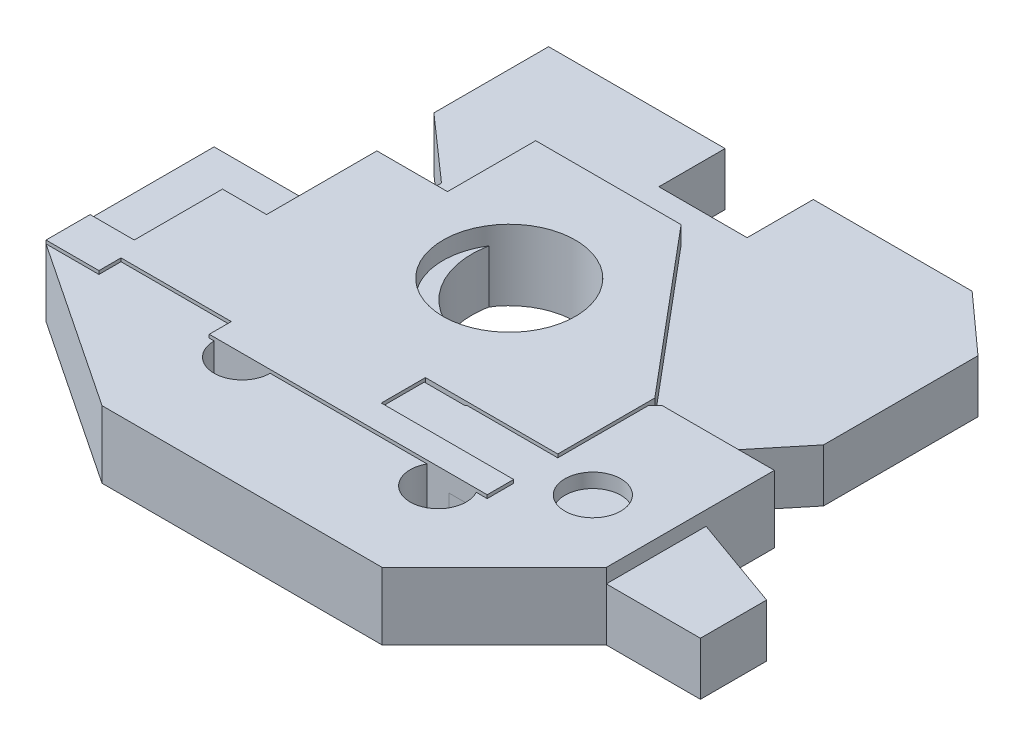
SolidWorks part; units mm, degrees
ref_plane "Front Plane" through (0, 0, 0) normal (0, 0, 1) x (1, 0, 0)
ref_plane "Top Plane" through (0, 0, 0) normal (0, 1, 0) x (1, 0, 0)
ref_plane "Right Plane" through (0, 0, 0) normal (1, 0, 0) x (0, 0, -1)
sketch "Sketch1" plane through (0, 0, 0) normal (0, 1, 0) x (1, 0, 0)
  line L0 (0, 0) -> (50, 0)
  line L1 (50, 0) -> (44, 9.42)
  line L2 (44, 9.42) -> (97.33, 9.42)
  line L3 (97.33, 9.42) -> (91.33, 0)
  line L4 (91.33, 0) -> (148.33, 0)
  line L5 (148.33, 0) -> (148.33, 15)
  line L6 (148.33, 15) -> (106.33, 30)
  line L7 (106.33, 30) -> (124.33, 51.92)
  line L8 (124.33, 51.92) -> (124.33, 86.92)
  line L9 (124.33, 86.92) -> (111, 98.92)
  line L10 (111, 98.92) -> (75, 98.92)
  line L11 (75, 98.92) -> (75, 83.92)
  line L12 (75, 83.92) -> (55, 83.92)
  line L13 (55, 83.92) -> (55, 98.92)
  line L14 (55, 98.92) -> (15, 98.92)
  line L15 (15, 98.92) -> (15, 72.92)
  line L16 (15, 72.92) -> (29.6447, 60)
  line L17 (29.6447, 60) -> (29.6447, 40)
  line L18 (29.6447, 40) -> (12, 20)
  line L19 (12, 20) -> (0, 20)
  line L20 (0, 20) -> (0, 0)
  circle A0 centre (65, 49.5) radius 18
  dimension "D24" = 36
  dimension "D1" = 50
  dimension "D2" = 57
  dimension "D3" = 15
  dimension "D4" = 20
  dimension "D5" = 40
  dimension "D6" = 26
  dimension "D7" = 20
  dimension "D8" = 12
  dimension "D9" = 6
  dimension "D10" = 6
  dimension "D11" = 148.33
  dimension "D12" = 9.42
  dimension "D13" = 30
  dimension "D14" = 98.92
  dimension "D15" = 47
  dimension "D16" = 12
  dimension "D17" = 13.33
  dimension "D18" = 109.33
  dimension "D19" = 20
  dimension "D20" = 20
  dimension "D21" = 42
  dimension "D22" = 15
  dimension "D23" = 15
  dimension "D25" = 50
  dimension "D26" = 49.5
extrude "Boss-Extrude1" add sketch "Sketch1" along normal blind 12
sketch "Sketch3" plane through (0, 0, 0) normal (0, 1, 0) x (1, 0, 0)
  line L0 (0, 0) -> (0, 38.1)
  line L1 (0, 38.1) -> (25.4, 38.1)
  line L2 (25.4, 38.1) -> (47.752, 15.748)
  line L3 (47.752, 15.748) -> (79.248, 15.748)
  line L4 (79.248, 15.748) -> (101.6, 38.1)
  line L5 (101.6, 38.1) -> (127, 38.1)
  line L6 (127, 38.1) -> (127, 0)
  line L7 (127, 0) -> (101.6, -25.4)
  line L8 (101.6, -25.4) -> (38.1, -25.4)
  line L9 (38.1, -25.4) -> (0, 0)
  circle A0 centre (19.05, 19.05) radius 6.35
  circle A1 centre (44.45, 0) radius 6.35
  circle A2 centre (91.948, -3.048) radius 6.35
  circle A3 centre (111.252, 12.7) radius 6.35
  point P19 (0, 0)
  point P20 (0, 0)
  point P21 (0, 0)
  point P22 (0, 0)
  point P23 (0, 0)
  point P24 (0, 0)
  point P25 (0, 0)
  dimension "D12" = 12.7
  dimension "D13" = 12.7
  dimension "D14" = 12.7
  dimension "D15" = 12.7
  dimension "D1" = 25.4
  dimension "D2" = 25.4
  dimension "D3" = 63.5
  dimension "D4" = 38.1
  dimension "D5" = 45
  dimension "D6" = 63.5
  dimension "D7" = 127
  dimension "D8" = 47.752
  dimension "D9" = 47.752
  dimension "D10" = 22.352
  dimension "D11" = 25.4
  dimension "D16" = 19.05
  dimension "D17" = 19.05
  dimension "D18" = 44.45
  dimension "D19" = 47.498
  dimension "D20" = 22.352
  dimension "D21" = 15.748
  dimension "D22" = 25.4
extrude "Boss-Extrude2" add sketch "Sketch3" along normal blind 15.24 separate body
sketch "Sketch5" plane through (0, 0, 0) normal (0, 1, 0) x (1, 0, 0)
  line L0 (0, 0) -> (12, 0)
  line L1 (12, 0) -> (12, 5)
  line L2 (12, 5) -> (37, 5)
  line L3 (37, 5) -> (37, 0)
  line L4 (37, 0) -> (100, 0)
  line L5 (100, 0) -> (100, 6)
  line L6 (100, 6) -> (70, 6)
  line L7 (70, 6) -> (70, 16)
  line L8 (70, 16) -> (100, 16)
  line L9 (100, 16) -> (100, 38)
  line L10 (100, 38) -> (68.9533, 75)
  line L11 (68.9533, 75) -> (36, 75)
  line L12 (36, 75) -> (36, 55)
  line L13 (36, 55) -> (20, 55)
  line L14 (20, 55) -> (20, 30)
  line L15 (20, 30) -> (10, 30)
  line L16 (10, 30) -> (10, 10)
  line L17 (10, 10) -> (0, 10)
  line L18 (0, 10) -> (0, 0)
  circle A0 centre (60, 45) radius 15
  dimension "D17" = 30
  dimension "D1" = 12
  dimension "D2" = 5
  dimension "D3" = 25
  dimension "D4" = 6
  dimension "D5" = 30
  dimension "D6" = 10
  dimension "D7" = 100
  dimension "D8" = 38
  dimension "D9" = 30
  dimension "D10" = 10
  dimension "D11" = 10
  dimension "D12" = 20
  dimension "D13" = 55
  dimension "D14" = 36
  dimension "D15" = 40
  dimension "D16" = 75
  dimension "D18" = 40
  dimension "D19" = 45
extrude "Boss-Extrude3" add sketch "Sketch5" along normal blind 16 separate body
